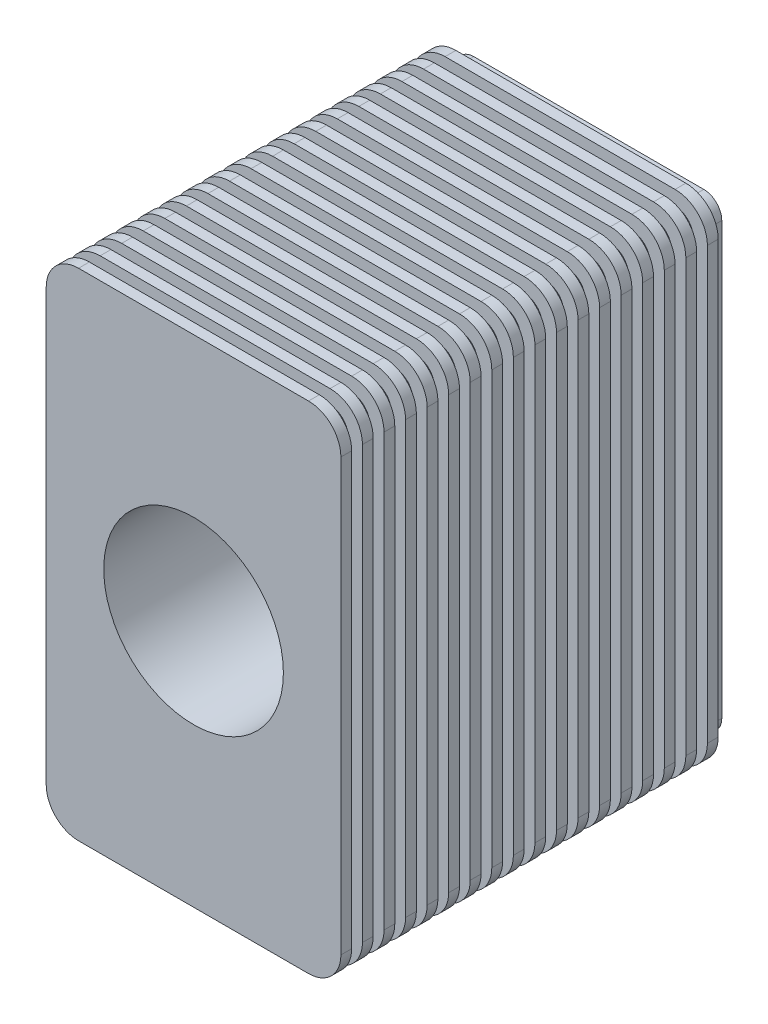
SolidWorks part; units mm, degrees
ref_plane "Front Plane" through (0, 0, 0) normal (0, 0, 1) x (1, 0, 0)
ref_plane "Top Plane" through (0, 0, 0) normal (0, 1, 0) x (1, 0, 0)
ref_plane "Right Plane" through (0, 0, 0) normal (1, 0, 0) x (0, 0, -1)
sketch "Sketch1" plane through (0, 0, 0) normal (0, 0, 1) x (1, 0, 0)
  line L0 (250, 0) -> (370, 0)
  line L1 (370, 0) -> (370, 600)
  line L2 (320, 650) -> (-320, 650)
  line L3 (-370, 600) -> (-370, 0)
  line L4 (-370, 0) -> (-250, 0)
  arc A0 (250, 0) -> (-250, 0) centre (0, 0) ccw
  arc A1 (370, 600) -> (320, 650) centre (320, 600) ccw
  arc A2 (-320, 650) -> (-370, 600) centre (-320, 600) ccw
  point P10 (370, 650)
  dimension "D1" = 500
  dimension "D5" = 50
  dimension "D2" = 120
  dimension "D3" = 120
  dimension "D4" = 650
extrude "Boss-Extrude1" add sketch "Sketch1" along normal mid plane 1100 contours L2 A2 L3 L4 A0 L0 L1 A1
sketch "Sketch2" plane through (0, 0, 550) normal (0, 0, 1) x (1, 0, 0)
  line L0 (320, 690) -> (-320, 690)
  line L1 (-410, 600) -> (-410, 0)
  line L4 (410, 0) -> (410, 600)
  line L5 (320, 650) -> (-320, 650)
  line L6 (-370, 600) -> (-370, 0)
  line L7 (-370, 0) -> (-250, 0)
  line L8 (250, 0) -> (370, 0)
  line L9 (370, 0) -> (370, 600)
  line L10 (320, 650) -> (-320, 650)
  line L11 (-370, 600) -> (-370, 0)
  line L12 (-410, 0) -> (-370, 0)
  line L13 (370, 0) -> (410, 0)
  line L14 (370, 0) -> (370, 600)
  line L15 (-370, 0) -> (-250, 0) construction
  line L16 (250, 0) -> (370, 0) construction
  line L17 (-410, -40) -> (-206.1553, -40) construction
  line L18 (-410, 600) -> (-410, -40) construction
  line L19 (206.1553, -40) -> (410, -40) construction
  line L20 (410, -40) -> (410, 600) construction
  arc A0 (-320, 690) -> (-410, 600) centre (-320, 600) ccw
  arc A2 (410, 600) -> (320, 690) centre (320, 600) ccw
  arc A3 (370, 600) -> (320, 650) centre (320, 600) ccw
  arc A4 (-320, 650) -> (-370, 600) centre (-320, 600) ccw
  arc A5 (250, 0) -> (-250, 0) centre (0, 0) ccw
  arc A6 (370, 600) -> (320, 650) centre (320, 600) ccw
  arc A7 (-320, 650) -> (-370, 600) centre (-320, 600) ccw
  arc A9 (206.1553, -40) -> (-206.1553, -40) centre (0, 0) ccw construction
  arc A13 (250, 0) -> (-250, 0) centre (0, 0) ccw construction
  dimension "D1" = 0
  dimension "D2" = 40
extrude "Boss-Extrude2" add sketch "Sketch2" against normal blind 30 separate body contours L1 L12 L11 A7 L10 A6 L14 L13 L4 A2 L0 A0
pattern_linear "LPattern1" count 18 spacing 60 along (0, 0, -1) of "Boss-Extrude2"
mirror "Mirror1" about plane through (250, 0, 550) normal (0, 1, 0) of "LPattern1", "Boss-Extrude2", "Boss-Extrude1"
